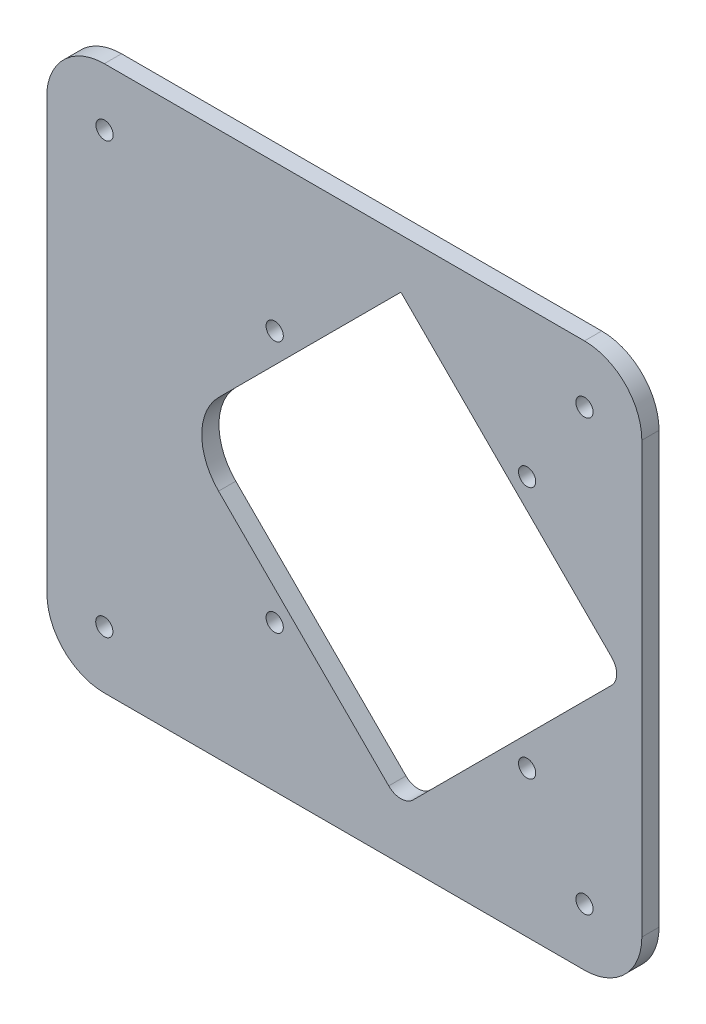
SolidWorks part; units mm, degrees
ref_plane "Front Plane" through (0, 0, 0) normal (0, 0, 1) x (1, 0, 0)
ref_plane "Top Plane" through (0, 0, 0) normal (0, 1, 0) x (1, 0, 0)
ref_plane "Right Plane" through (0, 0, 0) normal (1, 0, 0) x (0, 0, -1)
sketch "Model" plane through (0, 0, 0) normal (0, 0, 1) x (1, 0, 0)
  line L0 (75.7359, 67.6401) -> (82.0642, 73.9684)
  line L3 (117.2673, 85.8158) -> (33.5676, 85.8158)
  line L4 (23.5676, 11.7907) -> (23.5676, 67.2113)
  line L5 (23.5676, 0.8161) -> (23.5676, 11.7907)
  line L6 (23.5676, 67.2113) -> (23.5676, 76.8159)
  line L7 (127.2672, 11.5942) -> (127.2672, 49.316)
  line L8 (127.2672, 49.316) -> (127.2672, 75.8159)
  line L9 (127.2672, 0.8161) -> (127.2672, 11.5942)
  line L10 (33.5676, -9.1838) -> (117.2673, -9.1838)
  line L11 (63.2676, 16.3159) -> (107.2676, 16.3159) construction
  line L12 (107.2676, 60.3158) -> (107.2676, 16.3159) construction
  line L22 (122.0014, 40.4377) -> (89.4636, 72.9755)
  line L23 (87.3887, 1.5824) -> (122.0014, 36.1951)
  line L24 (53.4833, 31.2453) -> (83.1461, 1.5824)
  line L25 (85.2674, 77.1716) -> (82.0642, 73.9684)
  line L26 (89.4636, 72.9755) -> (85.2674, 77.1716)
  line L27 (75.7359, 67.6401) -> (53.3954, 45.2995)
  circle A0 centre (63.2676, 16.3159) radius 1.5
  circle A1 centre (117.2672, 75.8159) radius 1.5
  circle A2 centre (117.2672, 0.8161) radius 1.5
  circle A3 centre (33.61, 75.8159) radius 1.5
  circle A4 centre (33.5676, 0.8161) radius 1.5
  circle A5 centre (107.2676, 16.3159) radius 1.5
  circle A6 centre (63.2676, 60.3159) radius 1.5
  circle A7 centre (107.2676, 60.3158) radius 1.5
  arc A8 (127.2672, 75.8159) -> (117.2673, 85.8158) centre (117.2673, 75.816) ccw
  arc A9 (117.2673, -9.1838) -> (127.2672, 0.8161) centre (117.2672, 0.8161) ccw
  arc A10 (23.5676, 0.8161) -> (33.5676, -9.1838) centre (33.5676, 0.8162) ccw
  arc A11 (33.5676, 85.8158) -> (23.5676, 76.8159) centre (33.6101, 75.7131) ccw
  arc A12 (122.0014, 36.1951) -> (122.0014, 40.4377) centre (119.8801, 38.3164) ccw
  arc A13 (83.1461, 1.5824) -> (87.3887, 1.5824) centre (85.2674, 3.7037) ccw
  arc A14 (53.4833, 45.3874) -> (53.4833, 31.2453) centre (60.5543, 38.3164) ccw
  dimension "D1" = 44
  dimension "D2" = 44
extrude "Boss-Extrude1" add sketch "Model" along normal blind 3
